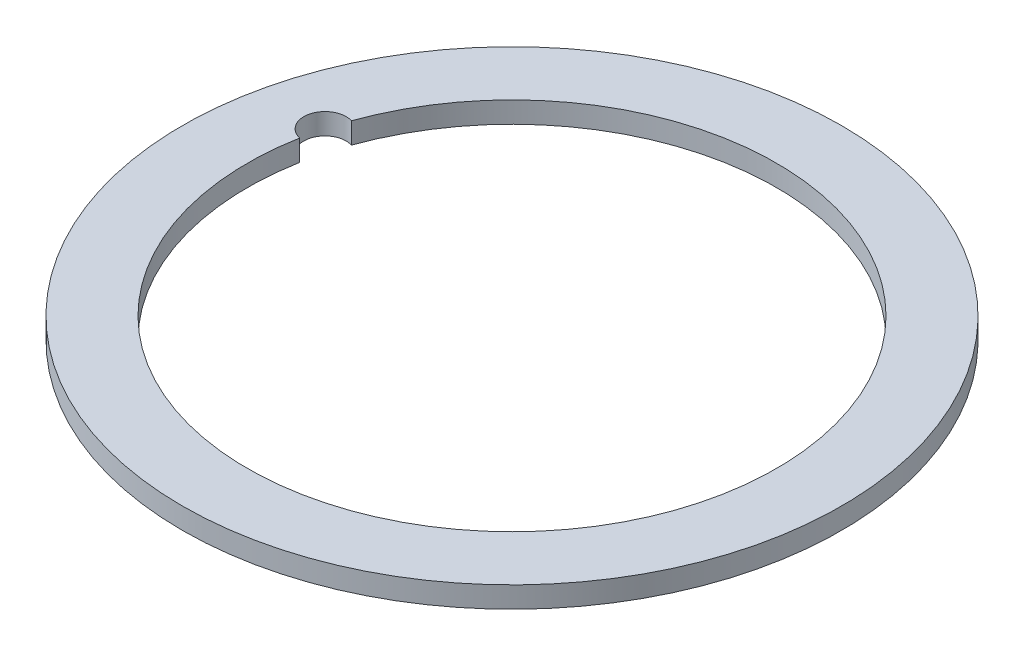
SolidWorks part; units mm, degrees
ref_plane "Front Plane" through (0, 0, 0) normal (0, 0, 1) x (1, 0, 0)
ref_plane "Top Plane" through (0, 0, 0) normal (0, 1, 0) x (1, 0, 0)
ref_plane "Right Plane" through (0, 0, 0) normal (1, 0, 0) x (0, 0, -1)
sketch "Sketch2" plane through (0, 0, 0) normal (0, 1, 0) x (1, 0, 0)
  circle A0 centre (0, 0) radius 49.53
  circle A1 centre (0, 0) radius 39.751
  dimension "D1" = 99.06
  dimension "D2" = 79.502
extrude "Boss-Extrude1" add sketch "Sketch2" along normal blind 3.175
sketch "Sketch3" plane through (0, 0, 0) normal (0, 1, 0) x (1, 0, 0)
  line L0 (0, 0) -> (-38.3965, 0) construction
  line L1 (-38.3965, 0) -> (-38.3965, 10.2883) construction
  line L2 (-38.3965, 10.2883) -> (0, 0) construction
  circle A0 centre (0, 0) radius 39.751 construction
  circle A1 centre (-38.3965, 10.2883) radius 3.175
  dimension "D2" = 6.35
  dimension "D1" = 15
extrude "Cut-Extrude1" cut sketch "Sketch3" along normal through all
